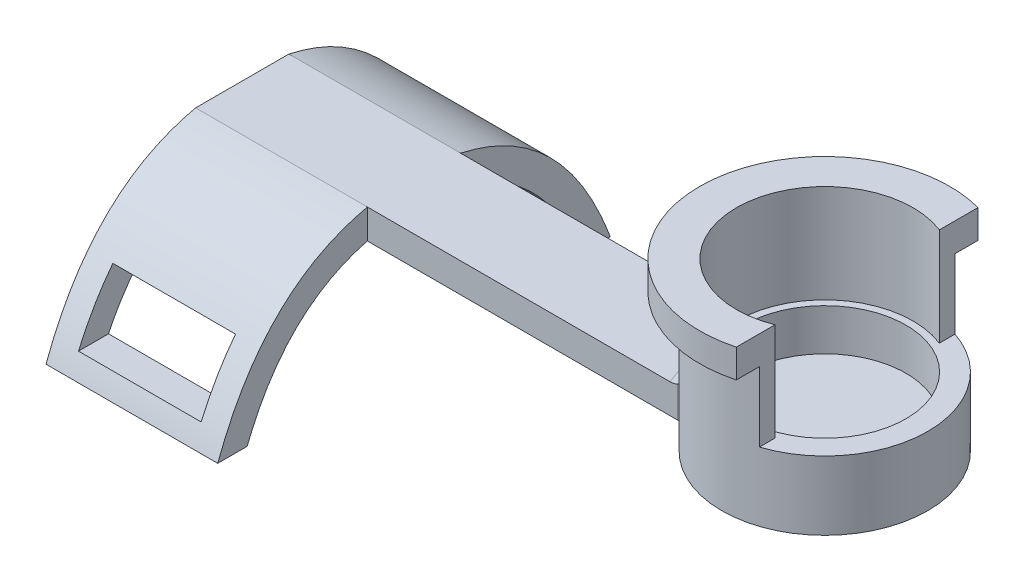
SolidWorks part; units mm, degrees
ref_plane "Front Plane" through (0, 0, 0) normal (0, 0, 1) x (1, 0, 0)
ref_plane "Top Plane" through (0, 0, 0) normal (0, 1, 0) x (1, 0, 0)
ref_plane "Right Plane" through (0, 0, 0) normal (1, 0, 0) x (0, 0, -1)
sketch "0.1mm fit for pot" plane through (0, 0, 0) normal (0, 1, 0) x (1, 0, 0)
  circle A1 centre (0, 0) radius 10.5
  dimension "D2" = 21
extrude "Boss-Extrude1" add sketch "0.1mm fit for pot" along normal blind 2.75
sketch "Sketch4" plane through (0, 2.75, 0) normal (0, 1, 0) x (1, 0, 0)
  circle A0 centre (0, 0) radius 8.275
  circle A1 centre (0, 0) radius 10.5 construction
  circle A2 centre (0, 0) radius 10.5
  dimension "D1" = 16.55
extrude "Boss-Extrude2" add sketch "Sketch4" along normal blind 4.25
sketch "Sketch5" plane through (0, 2.75, 0) normal (0, 1, 0) x (1, 0, 0)
  line L6 (-1, -8.2144) -> (-1, -7.0658)
  line L7 (-1, -7.0658) -> (0.9881, -7.0658)
  line L8 (0.9881, -7.0658) -> (0.9881, -8.2158)
  circle A0 centre (0, 0) radius 8.275 construction
  arc A1 (-1, -8.2144) -> (0.9881, -8.2158) centre (0, 0) ccw
  point P3 (0, -8.25)
  point P6 (0, -8.25)
  point P7 (0, -8.25)
  dimension "D1" = 1.15
extrude "Boss-Extrude3" add sketch "Sketch5" along normal blind 2
fillet "Fillet1" radius 0.25 5 edges at (-1, 4.75, 7.6401) (0.9881, 4.75, 7.6408) (0.9881, 3.75, 7.0658) (-0.006, 4.75, 7.0658) (-1, 3.75, 7.0658)
sketch "Sketch7" plane through (0, 7, 0) normal (0, 1, 0) x (1, 0, 0)
  line L0 (3.2996, 9.9681) -> (3.2996, 8.3733)
  line L1 (3.2996, -8.3733) -> (3.2996, -9.9681)
  arc A0 (3.2996, 9.9681) -> (3.2996, -9.9681) centre (0, 0) ccw
  arc A1 (3.2996, 8.3733) -> (3.2996, -8.3733) centre (0, 0) ccw
  dimension "D1" = 18
  dimension "D2" = 21
extrude "Boss-Extrude6" add sketch "Sketch7" along normal blind 10
sketch "Sketch8" plane through (0, 17, 0) normal (0, 1, 0) x (1, 0, 0)
  line L0 (3.2996, 12.3156) -> (3.2996, 9.9681)
  line L1 (3.2996, -9.9681) -> (3.2996, -12.3156)
  arc A0 (3.2996, 12.3156) -> (3.2996, -12.3156) centre (0, 0) ccw
  arc A1 (3.2996, 9.9681) -> (3.2996, -9.9681) centre (0, 0) ccw construction
  arc A2 (3.2996, 9.9681) -> (3.2996, -9.9681) centre (0, 0) ccw
  dimension "D1" = 2.25
extrude "Boss-Extrude7" add sketch "Sketch8" against normal blind 2.9
sketch "Sketch9" plane through (0, 0, 0) normal (0, -1, 0) x (1, 0, 0)
  line L3 (-9.3642, 4.75) -> (-59.3642, 4.75)
  line L5 (-9.3642, -4.75) -> (-59.3642, -4.75)
  line L6 (-59.3642, 4.75) -> (-59.3642, -4.75)
  circle A0 centre (0, 0) radius 10.5 construction
  arc A1 (-9.3642, 4.75) -> (-9.3642, -4.75) centre (0, 0) ccw
  point P10 (-5.25, 0)
  dimension "D1" = 50
extrude "Boss-Extrude8" add sketch "Sketch9" against normal blind 3
fillet "Fillet2" radius 1.5 3 edges at (-9.3642, 1.5, -4.75) (-9.3642, 1.5, 4.75) (-10.5, 3, 0)
sketch "Sketch10" plane through (-59.3642, 0, 0) normal (-1, 0, 0) x (0, 0, 1)
  line L0 (0, 3) -> (0, -12) construction
  line L1 (4.75, 3) -> (-4.75, 3) construction
  line L2 (20, -12) -> (-20, -12) construction
  line L3 (-20, -12) -> (-17, -12)
  line L4 (20, -12) -> (17, -12)
  line L5 (-4.75, 3) -> (4.75, 3)
  line L6 (4.75, 0) -> (-4.75, 0)
  spline S0 degree 2 poles (-17, -12) (-13.1347, -2.139) (-4.75, 0) knots 0 0 0 0.391544 0.391544 0.391544
  spline S1 degree 2 poles (-20, -12) (-15.2738, 0.6935) (-4.75, 3) knots 0 0 0 0.409146 0.409146 0.409146
  spline S2 degree 2 poles (4.75, 3) (15.2738, 0.6935) (20, -12) knots 0.590854 0.590854 0.590854 1 1 1
  spline S3 degree 2 poles (4.75, 0) (13.1347, -2.139) (17, -12) knots 0.608456 0.608456 0.608456 1 1 1
  point P8 (0, -12)
  dimension "D1" = 15
  dimension "D2" = 40
  dimension "D3" = 3
  dimension "D4" = 3
extrude "Boss-Extrude9" add sketch "Sketch10" against normal blind 17.5
sketch "Sketch12" plane through (0, 0, -4.75) normal (0, 0, -1) x (-1, 0, 0)
  line L0 (50.6142, -12) -> (50.6142, -10) construction
  line L1 (41.8642, -12) -> (59.3642, -12) construction
  line L2 (56.8642, -10) -> (44.3642, -10) construction
  line L4 (44.3642, -10) -> (56.8642, -10)
  line L5 (44.3642, -10) -> (44.3642, -4)
  line L6 (44.3642, -4) -> (56.8642, -4)
  line L7 (56.8642, -10) -> (56.8642, -4)
  point P7 (50.6142, -10)
  dimension "D1" = 6
extrude "Cut-Extrude2" cut sketch "Sketch12" against normal through all both and the other way through all
